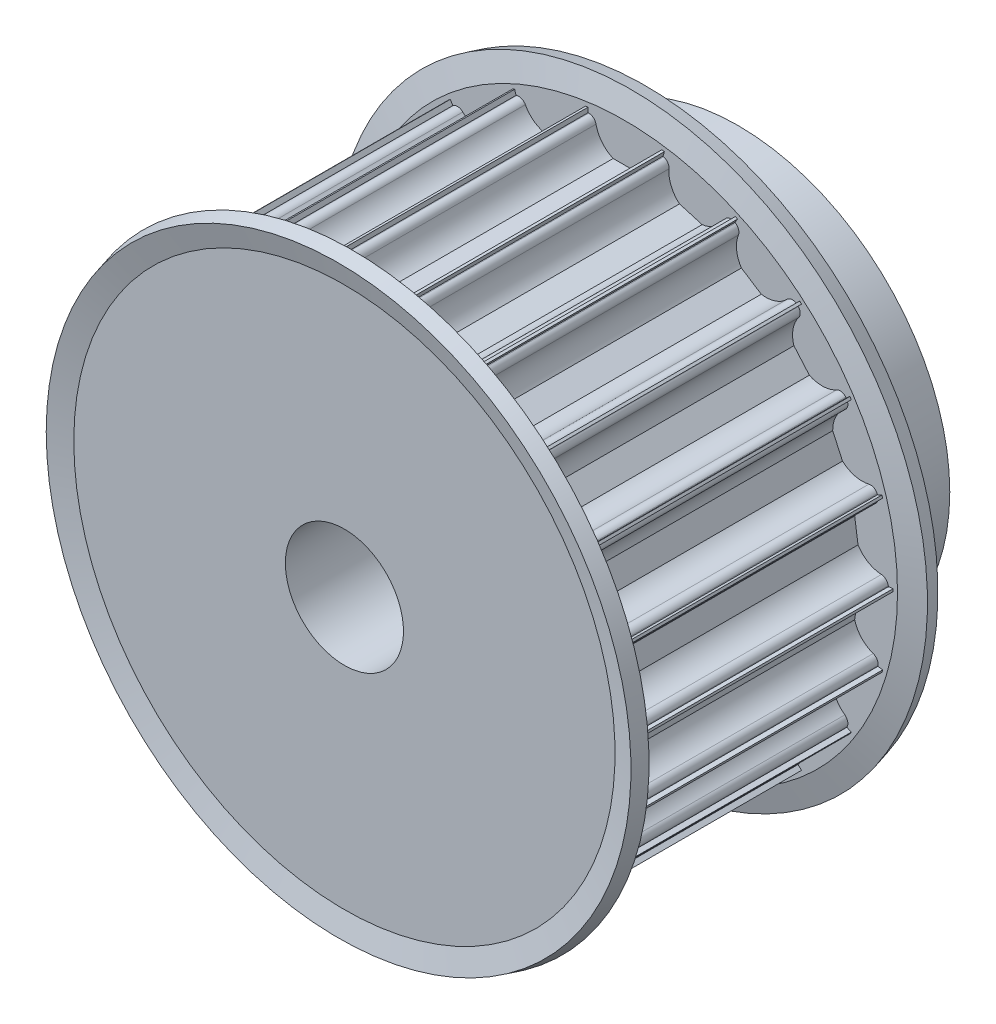
SolidWorks part; units mm, degrees
ref_plane "Alzado" through (0, 0, 0) normal (0, 0, 1) x (1, 0, 0)
ref_plane "Planta" through (0, 0, 0) normal (0, 1, 0) x (1, 0, 0)
ref_plane "Vista lateral" through (0, 0, 0) normal (1, 0, 0) x (0, 0, -1)
ref_axis "Eje1" through (0, 0, -88.99) along (0, 0, 1)
sketch "Croquis1" plane through (0, 0, 0) normal (1, 0, 0) x (0, 0, -1)
  line L0 (0, 6) -> (0, 27.25)
  line L1 (0, 27.25) -> (30, 27.25)
  line L2 (30, 27.25) -> (30, 21.5)
  line L3 (30, 21.5) -> (40, 21.5)
  line L4 (40, 21.5) -> (40, 6)
  line L5 (40, 6) -> (0, 6)
  line L6 (88.99, 0) -> (-88.99, 0) construction
  dimension "D1" = 6
  dimension "D2" = 21.25
  dimension "D3" = 30
  dimension "D4" = 10
  dimension "D5" = 15.5
revolve "Revolución1" add sketch "Croquis1" angle 360 about axis through (0, 0, -88.99) along (0, 0, 1)
sketch "Croquis2" plane through (0, 0, 0) normal (0, 0, 1) x (1, 0, 0)
  line L0 (3.6742, 26.5) -> (3.75, 26.5)
  line L1 (-3.75, 28.5) -> (3.75, 28.5)
  line L2 (-3.75, 28.5) -> (-3.75, 26.5)
  line L3 (-3.75, 26.5) -> (-3.6742, 26.5)
  line L4 (3.75, 28.5) -> (3.75, 26.5)
  line L5 (-1.199, 23.75) -> (1.199, 23.75)
  arc A0 (2.9394, 25.9) -> (1.199, 23.75) centre (0, 26.5) cw
  arc A1 (2.9394, 25.9) -> (3.6742, 26.5) centre (3.6742, 25.75) cw
  arc A2 (-2.9394, 25.9) -> (-3.6742, 26.5) centre (-3.6742, 25.75) ccw
  arc A3 (-1.199, 23.75) -> (-2.9394, 25.9) centre (0, 26.5) cw
  point P16 (3, 26.5)
  point P19 (-3, 26.5)
  dimension "D1" = 3
  dimension "D5" = 0.75
  dimension "D2" = 2
  dimension "D3" = 7.5
  dimension "D4" = 26.5
  dimension "D6" = 2.75
extrude "Cortar-Extruir1" cut sketch "Croquis2" against normal through all contours L1 L4 L0 A1 A0 L5 A3 A2 L3 L2
pattern_circular "MatrizC1" count 22 over 360 about axis through (0, 0, 0) along (0, 0, 1) of "Cortar-Extruir1"
sketch "Croquis4" plane through (0, 0, 0) normal (1, 0, 0) x (0, 0, -1)
  line L0 (0, 25.679) -> (0, 23.1257) construction
  line L1 (0, 22.6907) -> (1.5, 22.6907)
  line L2 (0, 22.6907) -> (0, 27.6907)
  line L3 (0, 27.6907) -> (1.5, 27.6907) construction
  line L4 (1.5, 22.6907) -> (1.5, 27.6907)
  line L5 (30, 26.9907) -> (0, 26.9907) construction
  line L6 (1.5, 27.6907) -> (0.0511, 27.3025) construction
  line L7 (1.5, 27.6907) -> (0.8569, 30.0907)
  line L8 (0.0511, 27.3025) -> (-0.592, 29.7025)
  line L9 (0.8569, 30.0907) -> (-0.592, 29.7025)
  line L10 (15, 34.5922) -> (15, -37.4964) construction
  line L11 (28.5, 27.6907) -> (29.9489, 27.3025) construction
  line L12 (30, 27.6907) -> (28.5, 27.6907) construction
  line L13 (29.1431, 30.0907) -> (30.592, 29.7025)
  line L14 (29.9489, 27.3025) -> (30.592, 29.7025)
  line L15 (28.5, 27.6907) -> (29.1431, 30.0907)
  line L16 (28.5, 22.6907) -> (28.5, 27.6907)
  line L17 (30, 22.6907) -> (30, 27.6907)
  line L18 (30, 22.6907) -> (28.5, 22.6907)
  line L19 (30, 26.9539) -> (0, 26.9539) construction
  dimension "D1" = 1.5
  dimension "D2" = 5
  dimension "D3" = 1.5
  dimension "D4" = 165
  dimension "D5" = 2.4
  dimension "D6" = 0.7
revolve "Revolución2" add sketch "Croquis4" angle 360 about axis through (0, 0, -88.99) along (0, 0, 1)
